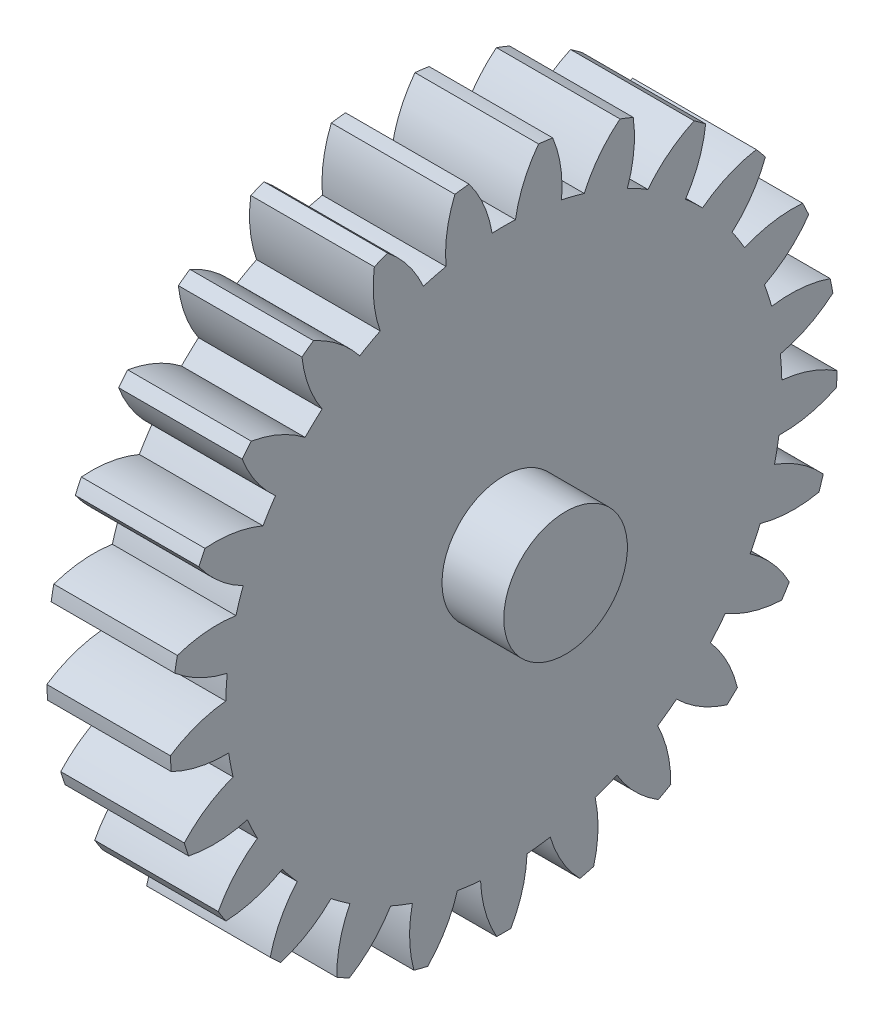
SolidWorks part; units mm, degrees
ref_plane "Front Plane" through (0, 0, 0) normal (0, 0, 1) x (1, 0, 0)
ref_plane "Top Plane" through (0, 0, 0) normal (0, 1, 0) x (1, 0, 0)
ref_plane "Right Plane" through (0, 0, 0) normal (1, 0, 0) x (0, 0, -1)
ref_plane "Plane1" through (-8.1841, 0, 0) normal (1, 0, 0) x (0, 0, -1)
sketch "Sketch1" plane through (-8.1841, 0, 0) normal (1, 0, 0) x (0, 0, -1)
  circle A0 centre (-4.758, 2.1882) radius 5
  arc A1 (-31.3817, 6.6805) -> (-27.1334, 4.544) centre (-24.8935, 14.2899) ccw
  arc A2 (-27.1334, 4.544) -> (-27.2522, 2.6554) centre (-4.758, 2.1882) ccw
  arc A3 (-27.2522, 2.6554) -> (-31.7348, 1.0682) centre (-26.2515, -7.2944) ccw
  arc A4 (-31.7348, 1.0682) -> (-31.6625, -0.0817) centre (-4.758, 2.1882) ccw
  arc A5 (-31.6625, -0.0817) -> (-27.0163, -1.0946) centre (-27.2705, 8.9022) ccw
  arc A6 (-27.0163, -1.0946) -> (-26.6617, -2.9534) centre (-4.758, 2.1882) ccw
  arc A7 (-26.6617, -2.9534) -> (-30.6087, -5.6055) centre (-23.218, -12.3417) ccw
  arc A8 (-30.6087, -5.6055) -> (-30.2527, -6.7013) centre (-4.758, 2.1882) ccw
  arc A9 (-30.2527, -6.7013) -> (-25.5006, -6.5268) centre (-28.2329, 3.0927) ccw
  arc A10 (-25.5006, -6.5268) -> (-24.6949, -8.239) centre (-4.758, 2.1882) ccw
  arc A11 (-24.6949, -8.239) -> (-27.8584, -11.7894) centre (-19.0246, -16.476) ccw
  arc A12 (-27.8584, -11.7894) -> (-27.241, -12.7622) centre (-4.758, 2.1882) ccw
  arc A13 (-27.241, -12.7622) -> (-22.6816, -11.4115) centre (-27.7204, -2.7737) ccw
  arc A14 (-22.6816, -11.4115) -> (-21.4754, -12.8695) centre (-4.758, 2.1882) ccw
  arc A15 (-21.4754, -12.8695) -> (-23.6566, -17.0951) centre (-13.9348, -19.4376) ccw
  arc A16 (-23.6566, -17.0951) -> (-22.8166, -17.8838) centre (-4.758, 2.1882) ccw
  arc A17 (-22.8166, -17.8838) -> (-18.7364, -15.4416) centre (-25.765, -8.3283) ccw
  arc A18 (-18.7364, -15.4416) -> (-17.2055, -16.5539) centre (-4.758, 2.1882) ccw
  arc A19 (-17.2055, -16.5539) -> (-18.2673, -21.1892) centre (-8.2684, -21.0404) ccw
  arc A20 (-18.2673, -21.1892) -> (-17.2576, -21.7442) centre (-4.758, 2.1882) ccw
  arc A21 (-17.2576, -21.7442) -> (-13.9129, -18.364) centre (-22.4896, -13.2222) ccw
  arc A22 (-13.9129, -18.364) -> (-12.1534, -19.0606) centre (-4.758, 2.1882) ccw
  arc A23 (-12.1534, -19.0606) -> (-12.0291, -23.8143) centre (-2.3814, -21.1836) ccw
  arc A24 (-12.0291, -23.8143) -> (-10.9131, -24.1009) centre (-4.758, 2.1882) ccw
  arc A25 (-10.9131, -24.1009) -> (-8.5141, -19.9951) centre (-18.1002, -17.1477) ccw
  arc A26 (-8.5141, -19.9951) -> (-6.6367, -20.2322) centre (-4.758, 2.1882) ccw
  arc A27 (-6.6367, -20.2322) -> (-5.3341, -24.8056) centre (3.3563, -19.8583) ccw
  arc A28 (-5.3341, -24.8056) -> (-4.1819, -24.8056) centre (-4.758, 2.1882) ccw
  arc A29 (-4.1819, -24.8056) -> (-2.8794, -20.2322) centre (-12.8724, -19.8583) ccw
  arc A30 (-2.8794, -20.2322) -> (-1.002, -19.9951) centre (-4.758, 2.1882) ccw
  arc A31 (-1.002, -19.9951) -> (1.3971, -24.1009) centre (8.5841, -17.1477) ccw
  arc A32 (1.3971, -24.1009) -> (2.5131, -23.8143) centre (-4.758, 2.1882) ccw
  arc A33 (2.5131, -23.8143) -> (2.6374, -19.0606) centre (-7.1347, -21.1836) ccw
  arc A34 (2.6374, -19.0606) -> (4.3968, -18.364) centre (-4.758, 2.1882) ccw
  arc A35 (4.3968, -18.364) -> (7.7415, -21.7442) centre (12.9736, -13.2222) ccw
  arc A36 (7.7415, -21.7442) -> (8.7512, -21.1892) centre (-4.758, 2.1882) ccw
  arc A37 (8.7512, -21.1892) -> (7.6894, -16.5539) centre (-1.2477, -21.0404) ccw
  arc A38 (7.6894, -16.5539) -> (9.2203, -15.4416) centre (-4.758, 2.1882) ccw
  arc A39 (9.2203, -15.4416) -> (13.3006, -17.8838) centre (16.2489, -8.3283) ccw
  arc A40 (13.3006, -17.8838) -> (14.1405, -17.0951) centre (-4.758, 2.1882) ccw
  arc A41 (14.1405, -17.0951) -> (11.9593, -12.8695) centre (4.4187, -19.4376) ccw
  arc A42 (11.9593, -12.8695) -> (13.1655, -11.4115) centre (-4.758, 2.1882) ccw
  arc A43 (13.1655, -11.4115) -> (17.7249, -12.7622) centre (18.2043, -2.7737) ccw
  arc A44 (17.7249, -12.7622) -> (18.3423, -11.7894) centre (-4.758, 2.1882) ccw
  arc A45 (18.3423, -11.7894) -> (15.1788, -8.239) centre (9.5085, -16.476) ccw
  arc A46 (15.1788, -8.239) -> (15.9845, -6.5268) centre (-4.758, 2.1882) ccw
  arc A47 (15.9845, -6.5268) -> (20.7366, -6.7013) centre (18.7169, 3.0927) ccw
  arc A48 (20.7366, -6.7013) -> (21.0927, -5.6055) centre (-4.758, 2.1882) ccw
  arc A49 (21.0927, -5.6055) -> (17.1456, -2.9534) centre (13.7019, -12.3417) ccw
  arc A50 (17.1456, -2.9534) -> (17.5002, -1.0946) centre (-4.758, 2.1882) ccw
  arc A51 (17.5002, -1.0946) -> (22.1464, -0.0817) centre (17.7544, 8.9022) ccw
  arc A52 (22.1464, -0.0817) -> (22.2187, 1.0682) centre (-4.758, 2.1882) ccw
  arc A53 (22.2187, 1.0682) -> (17.7361, 2.6554) centre (16.7354, -7.2944) ccw
  arc A54 (17.7361, 2.6554) -> (17.6173, 4.544) centre (-4.758, 2.1882) ccw
  arc A55 (17.6173, 4.544) -> (21.8656, 6.6805) centre (15.3775, 14.2899) ccw
  arc A56 (21.8656, 6.6805) -> (21.6497, 7.8122) centre (-4.758, 2.1882) ccw
  arc A57 (21.6497, 7.8122) -> (16.9132, 8.2348) centre (18.4184, -1.6513) ccw
  arc A58 (16.9132, 8.2348) -> (16.3285, 10.0345) centre (-4.758, 2.1882) ccw
  arc A59 (16.3285, 10.0345) -> (19.912, 13.1604) centre (11.7353, 18.9172) ccw
  arc A60 (19.912, 13.1604) -> (19.4214, 14.2029) centre (-4.758, 2.1882) ccw
  arc A61 (19.4214, 14.2029) -> (14.7287, 13.4342) centre (18.6451, 4.2331) ccw
  arc A62 (14.7287, 13.4342) -> (13.7147, 15.032) centre (-4.758, 2.1882) ccw
  arc A63 (13.7147, 15.032) -> (16.4083, 18.9508) centre (7.0568, 22.4933) ccw
  arc A64 (16.4083, 18.9508) -> (15.6739, 19.8386) centre (-4.758, 2.1882) ccw
  arc A65 (15.6739, 19.8386) -> (11.3197, 17.9271) centre (17.4013, 9.989) ccw
  arc A66 (11.3197, 17.9271) -> (9.9402, 19.2225) centre (-4.758, 2.1882) ccw
  arc A67 (9.9402, 19.2225) -> (11.5746, 23.6881) centre (1.6359, 24.7937) ccw
  arc A68 (11.5746, 23.6881) -> (10.6425, 24.3653) centre (-4.758, 2.1882) ccw
  arc A69 (10.6425, 24.3653) -> (6.9005, 21.431) centre (14.7652, 15.2547) ccw
  arc A70 (6.9005, 21.431) -> (5.2422, 22.3426) centre (-4.758, 2.1882) ccw
  arc A71 (5.2422, 22.3426) -> (5.7147, 27.0744) centre (-4.1867, 25.6736) ccw
  arc A72 (5.7147, 27.0744) -> (4.6434, 27.4985) centre (-4.758, 2.1882) ccw
  arc A73 (4.6434, 27.4985) -> (1.7487, 23.7258) centre (10.9023, 19.6994) ccw
  arc A74 (1.7487, 23.7258) -> (-0.0841, 24.1964) centre (-4.758, 2.1882) ccw
  arc A75 (-0.0841, 24.1964) -> (-0.8033, 28.897) centre (-10.0452, 25.0778) ccw
  arc A76 (-0.8033, 28.897) -> (-1.9464, 29.0414) centre (-4.758, 2.1882) ccw
  arc A77 (-1.9464, 29.0414) -> (-3.8119, 24.6673) centre (6.0555, 23.0438) ccw
  arc A78 (-3.8119, 24.6673) -> (-5.7042, 24.6673) centre (-4.758, 2.1882) ccw
  arc A79 (-5.7042, 24.6673) -> (-7.5697, 29.0414) centre (-15.5715, 23.0438) ccw
  arc A80 (-7.5697, 29.0414) -> (-8.7128, 28.897) centre (-4.758, 2.1882) ccw
  arc A81 (-8.7128, 28.897) -> (-9.4319, 24.1964) centre (0.5291, 25.0778) ccw
  arc A82 (-9.4319, 24.1964) -> (-11.2648, 23.7258) centre (-4.758, 2.1882) ccw
  arc A83 (-11.2648, 23.7258) -> (-14.1595, 27.4985) centre (-20.4184, 19.6994) ccw
  arc A84 (-14.1595, 27.4985) -> (-15.2308, 27.0744) centre (-4.758, 2.1882) ccw
  arc A85 (-15.2308, 27.0744) -> (-14.7583, 22.3426) centre (-5.3294, 25.6736) ccw
  arc A86 (-14.7583, 22.3426) -> (-16.4165, 21.431) centre (-4.758, 2.1882) ccw
  arc A87 (-16.4165, 21.431) -> (-20.1586, 24.3653) centre (-24.2813, 15.2547) ccw
  arc A88 (-20.1586, 24.3653) -> (-21.0907, 23.6881) centre (-4.758, 2.1882) ccw
  arc A89 (-21.0907, 23.6881) -> (-19.4563, 19.2225) centre (-11.152, 24.7937) ccw
  arc A90 (-19.4563, 19.2225) -> (-20.8358, 17.9271) centre (-4.758, 2.1882) ccw
  arc A91 (-20.8358, 17.9271) -> (-25.1899, 19.8386) centre (-26.9174, 9.989) ccw
  arc A92 (-25.1899, 19.8386) -> (-25.9244, 18.9508) centre (-4.758, 2.1882) ccw
  arc A93 (-25.9244, 18.9508) -> (-23.2308, 15.032) centre (-16.5729, 22.4933) ccw
  arc A94 (-23.2308, 15.032) -> (-24.2447, 13.4342) centre (-4.758, 2.1882) ccw
  arc A95 (-24.2447, 13.4342) -> (-28.9375, 14.2029) centre (-28.1612, 4.2331) ccw
  arc A96 (-28.9375, 14.2029) -> (-29.4281, 13.1604) centre (-4.758, 2.1882) ccw
  arc A97 (-29.4281, 13.1604) -> (-25.8446, 10.0345) centre (-21.2514, 18.9172) ccw
  arc A98 (-25.8446, 10.0345) -> (-26.4293, 8.2348) centre (-4.758, 2.1882) ccw
  arc A99 (-26.4293, 8.2348) -> (-31.1658, 7.8122) centre (-27.9345, -1.6513) ccw
  arc A100 (-31.1658, 7.8122) -> (-31.3817, 6.6805) centre (-4.758, 2.1882) ccw
extrude "Boss-Extrude1" add sketch "Sketch1" against normal blind 10
sketch "Sketch2" plane through (-18.1841, 0, 0) normal (-1, 0, 0) x (0, 0, 1)
  circle A0 centre (4.758, 2.1882) radius 5
extrude "Boss-Extrude2" add sketch "Sketch2" along normal blind 5 and the other way blind 15
